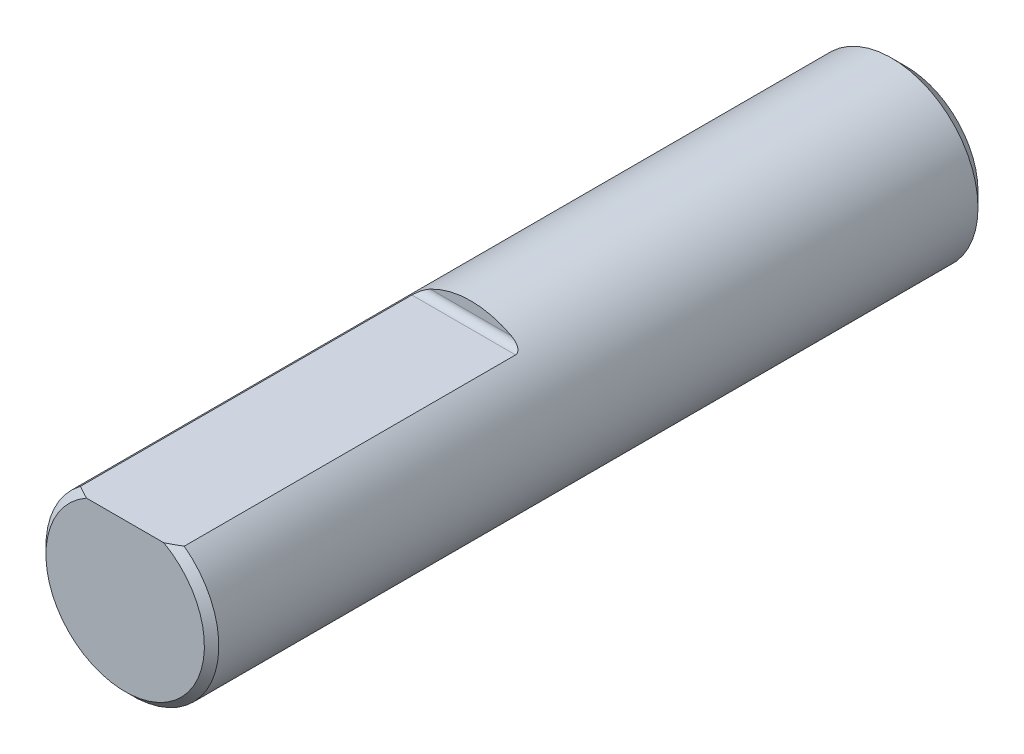
SolidWorks part; units mm, degrees
ref_plane "Alzado" through (0, 0, 0) normal (0, 0, 1) x (1, 0, 0)
ref_plane "Planta" through (0, 0, 0) normal (0, 1, 0) x (1, 0, 0)
ref_plane "Vista lateral" through (0, 0, 0) normal (1, 0, 0) x (0, 0, -1)
sketch "Croquis1" plane through (0, 0, 0) normal (0, 0, 1) x (1, 0, 0)
  circle A0 centre (0, 0) radius 3
  dimension "D1" = 6
extrude "Saliente-Extruir1" add sketch "Croquis1" along normal blind 27.1
sketch "Croquis2" plane through (0, 0, 27.1) normal (0, 0, 1) x (1, 0, 0)
  line L0 (0, -3) -> (0, 2.4) construction
  line L1 (-1.8, 2.4) -> (1.8, 2.4)
  circle A0 centre (0, 0) radius 3 construction
  arc A1 (1.8, 2.4) -> (-1.8, 2.4) centre (0, 0) ccw
  dimension "D1" = 6
  dimension "D2" = 5.4
extrude "Cortar-Extruir1" cut sketch "Croquis2" against normal blind 12
chamfer "Chaflán1" distance 0.25 angle 45 1 edges at (0, -3, 27.1)
sketch "Sketch1" plane through (0, 0, 0) normal (0, 0, -1) x (-1, 0, 0)
  line L0 (0, 0) -> (0, 0.75) construction
  line L1 (0, 0.75) -> (-0.6614, 0.75)
  line L2 (0, 0.75) -> (0.6614, 0.75)
  arc A0 (-0.6614, 0.75) -> (0.6614, 0.75) centre (0, 0) ccw
  dimension "D1" = 2
  dimension "D2" = 0.75
extrude "Cut-Extrude2" cut sketch "Sketch1" against normal blind 2.5
chamfer "Chamfer1" distance 0.5 angle 45 1 edges at (3, 0, 0)
fillet "Fillet1" radius 0.25 1 edges at (0, 2.4, 15.1)
